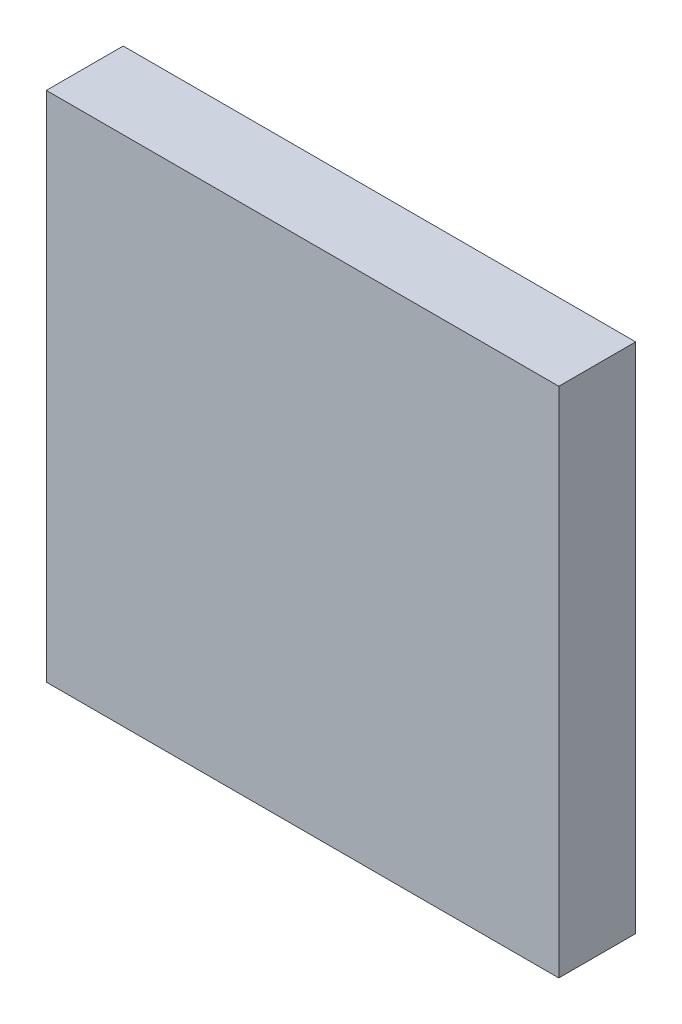
SolidWorks part; units mm, degrees
ref_plane "Front Plane" through (0, 0, 0) normal (0, 0, 1) x (1, 0, 0)
ref_plane "Top Plane" through (0, 0, 0) normal (0, 1, 0) x (1, 0, 0)
ref_plane "Right Plane" through (0, 0, 0) normal (1, 0, 0) x (0, 0, -1)
sketch "Sketch1" plane through (0, 0, 0) normal (0, 0, 1) x (1, 0, 0)
  line L0 (100, 200) -> (100, -13.0851) construction
  line L1 (0, 0) -> (200, 0)
  line L2 (0, 0) -> (0, 200)
  line L3 (0, 200) -> (200, 200)
  line L4 (200, 0) -> (200, 200)
  circle A0 centre (145, 130) radius 10
  circle A1 centre (55, 130) radius 10
  dimension "D5" = 20
  dimension "D1" = 200
  dimension "D2" = 200
  dimension "D3" = 70
  dimension "D4" = 45
extrude "Boss-Extrude1" add sketch "Sketch1" along normal blind 30
sketch "Sketch2" plane through (0, 0, 0) normal (0, 0, -1) x (-1, 0, 0)
  circle A0 centre (-145, 130) radius 10 construction
  circle A1 centre (-55, 130) radius 10 construction
  circle A2 centre (-145, 130) radius 10
  circle A3 centre (-55, 130) radius 10
extrude "Boss-Extrude2" add sketch "Sketch2" against normal blind 20 from offset 10 offset against normal yes
